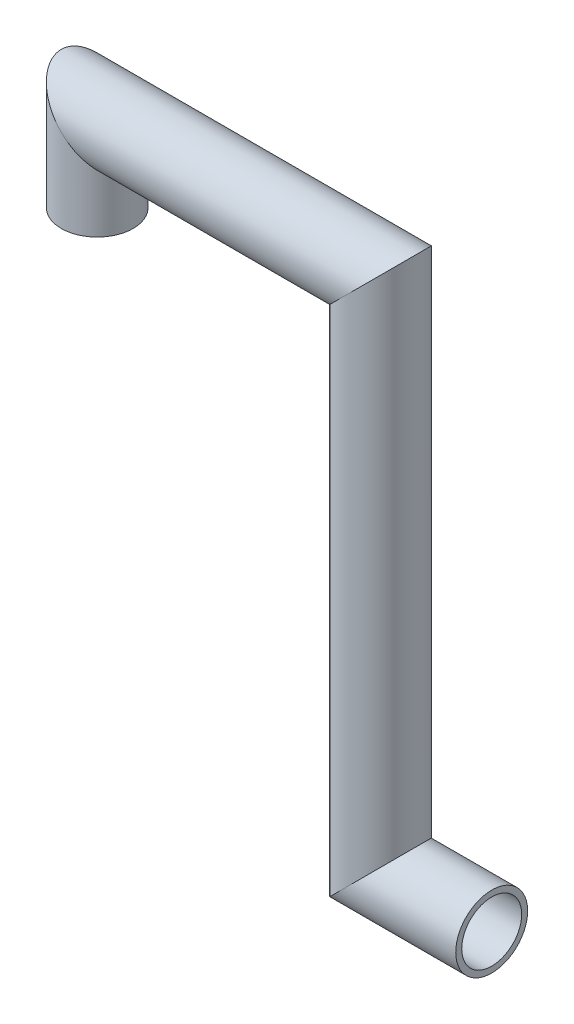
SolidWorks part; units mm, degrees
ref_plane "Front Plane" through (0, 0, 0) normal (0, 0, 1) x (1, 0, 0)
ref_plane "Top Plane" through (0, 0, 0) normal (0, 1, 0) x (1, 0, 0)
ref_plane "Right Plane" through (0, 0, 0) normal (1, 0, 0) x (0, 0, -1)
sketch "Sketch1" plane through (0, 0, 0) normal (0, 0, 1) x (1, 0, 0)
  line L10 (-329.074, 306.4071) -> (-329.074, 445.3278)
  line L11 (-329.074, 445.3278) -> (143.6099, 445.3278)
  line L12 (143.6099, 445.3278) -> (143.6099, -410.3278)
  line L13 (143.6099, -410.3278) -> (329.074, -410.3278)
ref_plane "Plane1" through (0, 306.4071, 0) normal (0, 1, 0) x (1, 0, 0)
sketch "Sketch8" plane through (0, 306.4071, 0) normal (0, 1, 0) x (1, 0, 0)
  circle A0 centre (-329.074, 0) radius 60
  dimension "D1" = 120
sweep "Sweep-Thin1" add profiles "Sketch8" path "Sketch1" parameters "D1"=10
